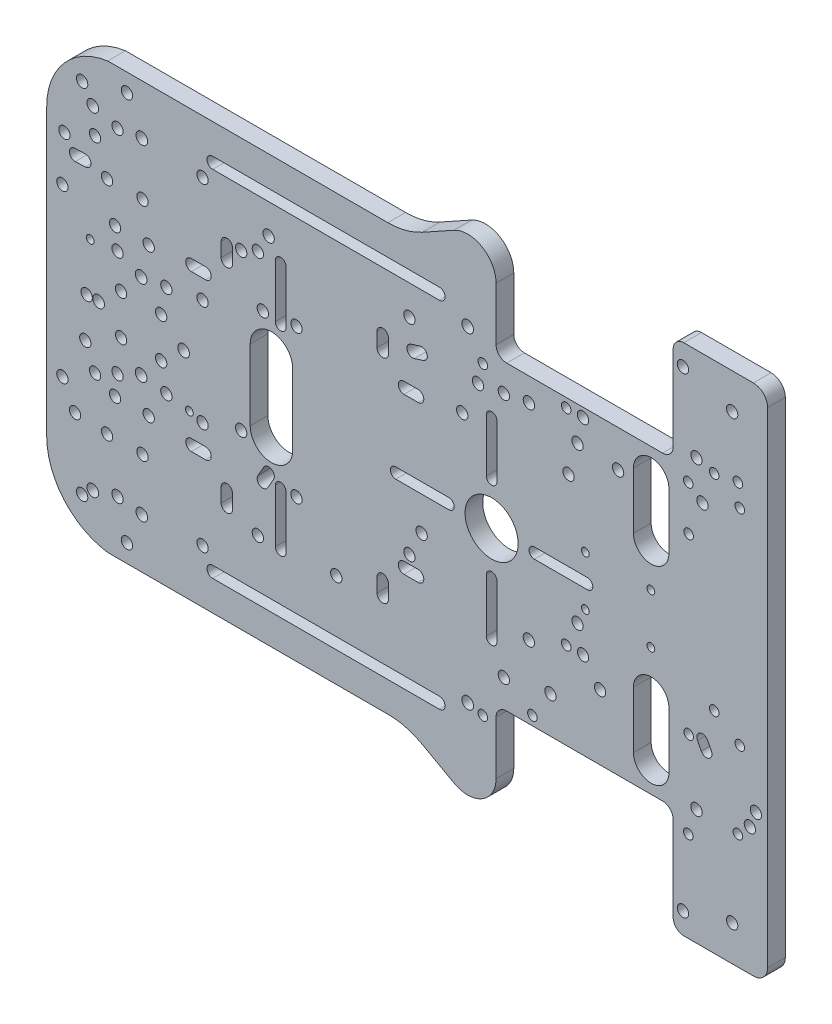
SolidWorks part; units mm, degrees
ref_plane "前视基准面" through (0, 0, 0) normal (0, 0, 1) x (1, 0, 0)
ref_plane "上视基准面" through (0, 0, 0) normal (0, 1, 0) x (1, 0, 0)
ref_plane "右视基准面" through (0, 0, 0) normal (1, 0, 0) x (0, 0, -1)
other "Configuration Table"
ref_plane "基准面1" through (0, 0, -5) normal (0, 0, -1) x (-1, 0, 0)
sketch "草图1" plane through (0, 0, -5) normal (0, 0, -1) x (-1, 0, 0)
  line L0 (-2.0302, 30.5969) -> (-4.5755, 31.4031)
  line L1 (-3.6092, 34.4537) -> (-1.064, 33.6476)
  line L2 (93.6948, 30.901) -> (90.7957, 31.001)
  line L3 (90.906, 34.199) -> (93.8052, 34.099)
  line L4 (-85.8731, -23.3852) -> (-84.789, -21.2965)
  line L5 (-81.9488, -22.7705) -> (-83.0328, -24.8593)
  line L6 (40.4887, -17.2053) -> (42.1253, -20.0649)
  line L7 (39.3479, -21.6544) -> (37.7113, -18.7947)
  line L8 (-63.8826, 34.7969) -> (-63.8826, 18.7969)
  line L9 (-73.8826, 18.7969) -> (-73.8826, 34.7969)
  line L10 (-73.8826, -34.7969) -> (-73.8826, -18.7969)
  line L11 (-63.8826, -18.7969) -> (-63.8826, -34.7969)
  line L12 (-35.9068, -1.5) -> (-50.9068, -1.5)
  line L13 (-50.9068, 1.5) -> (-35.9068, 1.5)
  line L14 (-11.7709, 1.5) -> (3.2291, 1.5)
  line L15 (3.2291, -1.5) -> (-11.7709, -1.5)
  line L16 (-25.3389, 12.0679) -> (-25.3389, 27.0679)
  line L17 (-22.3389, 27.0679) -> (-22.3389, 12.0679)
  line L18 (-25.3389, -27.0679) -> (-25.3389, -12.0679)
  line L19 (-22.3389, -12.0679) -> (-22.3389, -27.0679)
  line L20 (37.2135, -20) -> (37.2135, -35)
  line L21 (34.2135, -35) -> (34.2135, -20)
  line L22 (44.3046, 11) -> (44.3046, -9)
  line L23 (32.3046, -9) -> (32.3046, 11)
  line L24 (34.2135, 20) -> (34.2135, 35)
  line L25 (37.2135, 35) -> (37.2135, 20)
  line L27 (-25.0983, 69.5) -> (-25.0983, 45.53)
  line L28 (-28.0983, 42.53) -> (-72.0983, 42.53)
  line L29 (-75.0983, 45.53) -> (-75.0983, 69.5)
  line L30 (-78.0983, 72.5) -> (-81.75, 72.5)
  line L31 (-101.75, 52.5) -> (-101.75, -52.5)
  line L32 (-81.75, -72.5) -> (-78.0983, -72.5)
  line L33 (-75.0983, -69.5) -> (-75.0983, -45.53)
  line L34 (-72.0983, -42.53) -> (-28.0983, -42.53)
  line L35 (-25.0983, -45.53) -> (-25.0983, -69.5)
  line L38 (101.75, -40.2763) -> (101.75, 40.2763)
  line L40 (-81.75, 72.5) -> (-101.75, 72.5)
  line L41 (-101.75, 72.5) -> (-101.75, 52.5)
  line L42 (-101.75, -52.5) -> (-101.75, -72.5)
  line L43 (-101.75, -72.5) -> (-81.75, -72.5)
  line L44 (84.5216, 60.0833) -> (0.2583, 60.0833)
  line L46 (-22.0983, 72.5) -> (0.2583, 60.0833)
  line L47 (55, 0) -> (-55, 0) construction
  line L48 (-22.0983, -72.5) -> (0.2583, -60.0833)
  line L49 (-25.0983, -69.5) -> (-25.0983, -74.1662)
  line L50 (-22.0983, -72.5) -> (-25.0983, -74.1662)
  line L51 (84.5216, -60.0833) -> (0.2583, -60.0833)
  line L52 (-25.0983, 69.5) -> (-25.0983, 74.1662)
  line L53 (-22.0983, 72.5) -> (-25.0983, 74.1662)
  circle A0 centre (-27.2987, -34.7189) radius 1.6
  circle A1 centre (42.1392, -34.7189) radius 1.6
  circle A2 centre (42.1392, 34.7189) radius 1.6
  circle A3 centre (-27.2987, 34.7189) radius 1.6
  circle A4 centre (81.75, -45) radius 1.6
  circle A5 centre (88.1, -18) radius 1.6
  circle A6 centre (79.101, -55) radius 1.6
  circle A7 centre (93.75, -30.5) radius 1.6
  circle A8 centre (91.75, -49.5) radius 1.6
  circle A9 centre (-4.0924, -11.0716) radius 1.6
  circle A10 centre (-0.65, -18) radius 1.6
  circle A11 centre (31.2366, -19.8597) radius 1.6
  circle A12 centre (20, -33.5) radius 1.6
  circle A13 centre (-21.3568, -46.958) radius 1.35
  circle A14 centre (57.75, -45) radius 1.6
  circle A15 centre (31.2366, 21.8597) radius 1.6
  circle A16 centre (46.8508, 32.6) radius 1.6
  circle A17 centre (39.1, 40) radius 1.6
  circle A18 centre (-15.5471, 24.1222) radius 1.6
  circle A19 centre (-21.3568, 39.042) radius 1.35
  circle A20 centre (-20, 33.5) radius 1.6
  circle A21 centre (-0.65, 40) radius 1.6
  arc A22 (-4.5755, 31.4031) -> (-3.6092, 34.4537) centre (-4.0924, 32.9284) cw
  arc A23 (-1.064, 33.6476) -> (-2.0302, 30.5969) centre (-1.5471, 32.1222) cw
  circle A24 centre (57.75, -15) radius 1.6
  circle A25 centre (81.75, -15) radius 1.6
  circle A26 centre (90.8508, -11.4) radius 1.6
  circle A27 centre (57.75, 45) radius 1.6
  circle A28 centre (81.75, 45) radius 1.6
  circle A29 centre (88.1, 40) radius 1.6
  circle A30 centre (81.75, 15) radius 1.6
  circle A31 centre (57.75, 15) radius 1.6
  circle A32 centre (46.8508, -11.4) radius 1.6
  circle A33 centre (96.75, 36.5) radius 1.6
  circle A34 centre (79.101, 55) radius 1.6
  circle A35 centre (91.75, 51.5) radius 1.6
  arc A36 (93.8052, 34.099) -> (93.6948, 30.901) centre (93.75, 32.5) cw
  arc A37 (90.7957, 31.001) -> (90.906, 34.199) centre (90.8508, 32.6) cw
  circle A38 centre (-68.8, -6.5997) radius 1.1
  circle A39 centre (-68.8, 7.4003) radius 1.1
  circle A40 centre (-79.4702, 26.4708) radius 1.35
  circle A41 centre (-48.0924, 32.9284) radius 1.6
  circle A42 centre (-59.5471, 32.1222) radius 1.6
  circle A43 centre (-93.9, 40) radius 1.35
  circle A44 centre (-79.3568, 39.042) radius 1.35
  circle A45 centre (-44.9, 40) radius 1.35
  circle A46 centre (-49.65, 40) radius 1.6
  circle A47 centre (-91.75, 62.5) radius 1.6
  circle A48 centre (-83.3689, 35.9664) radius 1.6
  circle A49 centre (-77.8574, 66.5) radius 1.6
  circle A50 centre (-86.675, 44.8459) radius 1.35
  circle A51 centre (-79.3568, -46.958) radius 1.35
  circle A52 centre (-81.6777, -39.8031) radius 1.6
  circle A53 centre (-35.3568, -39.958) radius 1.35
  circle A54 centre (-34.369, -22.0335) radius 1.6
  circle A55 centre (-93.3568, -39.958) radius 1.35
  circle A56 centre (-91.75, -62.5) radius 1.6
  circle A57 centre (-77.8574, -66.5) radius 1.6
  circle A58 centre (-40.4529, -32.1222) radius 1.6
  circle A59 centre (-98.4529, -32.1222) radius 1.6
  arc A60 (-84.789, -21.2965) -> (-81.9488, -22.7705) centre (-83.3689, -22.0335) cw
  arc A61 (-83.0328, -24.8593) -> (-85.8731, -23.3852) centre (-84.4529, -24.1222) cw
  circle A62 centre (-79.4702, -22.5291) radius 1.35
  circle A63 centre (-96.75, -36.5) radius 1.6
  circle A64 centre (-93.3568, 46.042) radius 1.35
  circle A65 centre (-81.6777, 46.1969) radius 1.6
  circle A66 centre (-86.675, -13.154) radius 1.35
  circle A67 centre (-93.9, -18) radius 1.35
  circle A68 centre (-48.0924, -11.0716) radius 1.6
  circle A69 centre (-50.3001, -6.5997) radius 1.1
  circle A70 centre (-50.3001, 7.4003) radius 1.1
  circle A71 centre (-49.65, -18) radius 1.6
  circle A72 centre (-45.5471, 24.1222) radius 1.6
  circle A73 centre (-44.9, -18) radius 1.35
  circle A74 centre (-54.4529, -24.1222) radius 1.6
  circle A75 centre (-34.369, 35.9664) radius 1.6
  arc A76 (42.1253, -20.0649) -> (39.3479, -21.6544) centre (40.7366, -20.8597) cw
  arc A77 (37.7113, -18.7947) -> (40.4887, -17.2053) centre (39.1, -18) cw
  circle A78 centre (80.7531, 5.6569) radius 1.6
  circle A79 centre (82.4559, 20.8597) radius 1.6
  circle A80 centre (89.4709, 14.0014) radius 1.1
  circle A81 centre (67.9702, 12.9897) radius 1.6
  circle A82 centre (97.3184, 23.5) radius 1.6
  circle A83 centre (40.7366, 20.8597) radius 1.6
  circle A84 centre (72.9559, 20.8597) radius 1.6
  circle A85 centre (74.7057, -31.2) radius 1.6
  circle A86 centre (72.9559, -20.8597) radius 1.6
  circle A87 centre (74.7057, 31.2) radius 1.6
  circle A88 centre (67.9702, -12.9897) radius 1.6
  circle A89 centre (69.4394, 5.6569) radius 1.6
  circle A90 centre (80.7531, -5.6569) radius 1.6
  circle A91 centre (84.7052, -31.2) radius 1.6
  circle A92 centre (90.4702, 0.0007) radius 1.6
  circle A93 centre (69.4394, -5.6569) radius 1.6
  circle A94 centre (84.7052, 31.2) radius 1.6
  circle A95 centre (82.4559, -20.8597) radius 1.6
  circle A96 centre (61.4695, -14) radius 1.1
  circle A97 centre (97.3184, -23.5) radius 1.6
  arc A98 (-73.8826, 34.7969) -> (-63.8826, 34.7969) centre (-68.8826, 34.7969) cw
  arc A99 (-63.8826, 18.7969) -> (-73.8826, 18.7969) centre (-68.8826, 18.7969) cw
  arc A100 (-63.8826, -34.7969) -> (-73.8826, -34.7969) centre (-68.8826, -34.7969) cw
  arc A101 (-73.8826, -18.7969) -> (-63.8826, -18.7969) centre (-68.8826, -18.7969) cw
  arc A102 (-50.9068, -1.5) -> (-50.9068, 1.5) centre (-50.9068, 0) cw
  arc A103 (-35.9068, 1.5) -> (-35.9068, -1.5) centre (-35.9068, 0) cw
  arc A104 (3.2291, 1.5) -> (3.2291, -1.5) centre (3.2291, 0) cw
  arc A105 (-11.7709, -1.5) -> (-11.7709, 1.5) centre (-11.7709, 0) cw
  circle A106 centre (-23.8389, 0) radius 7.5
  arc A107 (-25.3389, 27.0679) -> (-22.3389, 27.0679) centre (-23.8389, 27.0679) cw
  arc A108 (-22.3389, 12.0679) -> (-25.3389, 12.0679) centre (-23.8389, 12.0679) cw
  arc A109 (-25.3389, -12.0679) -> (-22.3389, -12.0679) centre (-23.8389, -12.0679) cw
  arc A110 (-22.3389, -27.0679) -> (-25.3389, -27.0679) centre (-23.8389, -27.0679) cw
  arc A111 (37.2135, -35) -> (34.2135, -35) centre (35.7135, -35) cw
  arc A112 (34.2135, -20) -> (37.2135, -20) centre (35.7135, -20) cw
  arc A113 (32.3046, 11) -> (44.3046, 11) centre (38.3046, 11) cw
  arc A114 (44.3046, -9) -> (32.3046, -9) centre (38.3046, -9) cw
  arc A115 (34.2135, 35) -> (37.2135, 35) centre (35.7135, 35) cw
  arc A116 (37.2135, 20) -> (34.2135, 20) centre (35.7135, 20) cw
  arc A118 (-25.0983, 45.53) -> (-28.0983, 42.53) centre (-28.0983, 45.53) cw
  arc A119 (-72.0983, 42.53) -> (-75.0983, 45.53) centre (-72.0983, 45.53) cw
  arc A120 (-75.0983, 69.5) -> (-78.0983, 72.5) centre (-78.0983, 69.5) ccw
  arc A123 (-78.0983, -72.5) -> (-75.0983, -69.5) centre (-78.0983, -69.5) ccw
  arc A124 (-75.0983, -45.53) -> (-72.0983, -42.53) centre (-72.0983, -45.53) cw
  arc A125 (-28.0983, -42.53) -> (-25.0983, -45.53) centre (-28.0983, -45.53) cw
  arc A128 (84.5216, -60.0833) -> (101.75, -40.2763) centre (81.75, -40.2763) ccw
  arc A129 (101.75, 40.2763) -> (84.5216, 60.0833) centre (81.75, 40.2763) ccw
  dimension "D1" = 180
extrude "凸台-拉伸1" add sketch "草图1" against normal blind 5
sketch "草图2" plane through (0, 0, -5) normal (0, 0, -1) x (-1, 0, 0)
  circle A0 centre (75.0963, 12) radius 1.65
  circle A1 centre (87.0963, 0) radius 1.65
  circle A2 centre (75.0963, -12) radius 1.65
  circle A3 centre (63.0963, 0) radius 1.65
extrude "切除-拉伸1" cut sketch "草图2" against normal blind 10
sketch "草图3" plane through (0, 0, -5) normal (0, 0, -1) x (-1, 0, 0)
  circle A0 centre (88.75, 47) radius 1.65
  circle A1 centre (88.75, -47) radius 1.65
extrude "切除-拉伸2" cut sketch "草图3" against normal blind 10
fillet "圆角1" radius 4 2 edges at (101.75, -72.5, -2.5) (101.75, 72.5, -2.5)
fillet "圆角2" radius 8 2 edges at (25.0983, 74.1662, -2.5) (25.0983, -74.1662, -2.5)
fillet "圆角3" radius 20 2 edges at (-0.2583, -60.0833, -2.5) (-0.2583, 60.0833, -2.5)
sketch "草图4" plane through (0, 0, -5) normal (0, 0, -1) x (-1, 0, 0)
  line L0 (101.75, 0) -> (-23.8389, 0) construction
  line L1 (6.9017, 32) -> (6.9017, 28) construction
  line L2 (-25.0983, 60.572) -> (-25.0983, 45.53) construction
  line L3 (74.9017, -46) -> (-17.0983, -46) construction
  line L4 (74.9017, -46) -> (74.9017, 46) construction
  line L5 (74.9017, 46) -> (-17.0983, 46) construction
  line L6 (-17.0983, -46) -> (-17.0983, 46) construction
  line L7 (28.9017, 46) -> (28.9017, -46) construction
  line L8 (101.75, -40.2763) -> (101.75, 40.2763) construction
  line L9 (8.5017, 32) -> (8.5017, 28)
  line L10 (6.9017, 32) -> (50.9017, 32) construction
  line L11 (6.9017, 32) -> (6.9017, -32) construction
  line L12 (6.9017, -32) -> (50.9017, -32) construction
  line L13 (50.9017, 32) -> (50.9017, -32) construction
  line L14 (28.9017, -32) -> (28.9017, 32) construction
  line L16 (-3.0983, 22) -> (60.9017, 22) construction
  line L17 (-3.0983, 22) -> (-3.0983, -22) construction
  line L18 (-3.0983, -22) -> (60.9017, -22) construction
  line L19 (60.9017, 22) -> (60.9017, -22) construction
  line L20 (28.9017, -22) -> (28.9017, 22) construction
  line L21 (-3.0983, 0) -> (60.9017, 0) construction
  line L22 (6.9017, 16.0659) -> (6.9017, -16.0659) construction
  line L24 (50.9017, 16.0659) -> (50.9017, -16.0659) construction
  line L25 (28.9017, -16.0659) -> (28.9017, 16.0659) construction
  line L26 (6.9017, 0) -> (50.9017, 0) construction
  line L27 (5.3017, 32) -> (5.3017, 28)
  line L28 (-3.0983, 22) -> (0.9017, 22) construction
  line L29 (-3.0983, 23.6) -> (0.9017, 23.6)
  line L30 (-3.0983, 20.4) -> (0.9017, 20.4)
  line L31 (60.9017, 22) -> (56.9017, 22) construction
  line L32 (60.9017, 23.6) -> (56.9017, 23.6)
  line L33 (60.9017, 20.4) -> (56.9017, 20.4)
  line L34 (50.9017, 32) -> (50.9017, 28) construction
  line L35 (49.3017, 32) -> (49.3017, 28)
  line L36 (52.5017, 32) -> (52.5017, 28)
  line L37 (60.9017, -22) -> (56.9017, -22) construction
  line L38 (60.9017, -23.6) -> (56.9017, -23.6)
  line L39 (60.9017, -20.4) -> (56.9017, -20.4)
  line L40 (50.9017, -32) -> (50.9017, -28) construction
  line L41 (49.3017, -32) -> (49.3017, -28)
  line L42 (52.5017, -32) -> (52.5017, -28)
  line L43 (-3.0983, -22) -> (0.9017, -22) construction
  line L44 (-3.0983, -23.6) -> (0.9017, -23.6)
  line L45 (-3.0983, -20.4) -> (0.9017, -20.4)
  line L46 (6.9017, -32) -> (6.9017, -28) construction
  line L47 (8.5017, -32) -> (8.5017, -28)
  line L48 (5.3017, -32) -> (5.3017, -28)
  circle A0 centre (-17.0983, 46) radius 1.65
  arc A2 (8.5017, 32) -> (5.3017, 32) centre (6.9017, 32) ccw
  circle A6 centre (74.9017, 46) radius 1.65
  circle A7 centre (74.9017, -46) radius 1.65
  circle A12 centre (-17.0983, -46) radius 1.65
  arc A13 (5.3017, 28) -> (8.5017, 28) centre (6.9017, 28) ccw
  arc A14 (-3.0983, 23.6) -> (-3.0983, 20.4) centre (-3.0983, 22) ccw
  arc A15 (0.9017, 20.4) -> (0.9017, 23.6) centre (0.9017, 22) ccw
  arc A16 (60.9017, 23.6) -> (60.9017, 20.4) centre (60.9017, 22) cw
  arc A17 (56.9017, 20.4) -> (56.9017, 23.6) centre (56.9017, 22) cw
  arc A18 (49.3017, 32) -> (52.5017, 32) centre (50.9017, 32) cw
  arc A19 (52.5017, 28) -> (49.3017, 28) centre (50.9017, 28) cw
  arc A20 (60.9017, -23.6) -> (60.9017, -20.4) centre (60.9017, -22) ccw
  arc A21 (56.9017, -20.4) -> (56.9017, -23.6) centre (56.9017, -22) ccw
  arc A22 (49.3017, -32) -> (52.5017, -32) centre (50.9017, -32) ccw
  arc A23 (52.5017, -28) -> (49.3017, -28) centre (50.9017, -28) ccw
  arc A24 (-3.0983, -23.6) -> (-3.0983, -20.4) centre (-3.0983, -22) cw
  arc A25 (0.9017, -20.4) -> (0.9017, -23.6) centre (0.9017, -22) cw
  arc A26 (8.5017, -32) -> (5.3017, -32) centre (6.9017, -32) cw
  arc A27 (5.3017, -28) -> (8.5017, -28) centre (6.9017, -28) cw
  point P2 (6.9017, 30)
  point P5 (28.9017, 0)
  point P11 (28.9017, 0)
  point P15 (28.9017, 0)
  point P27 (-1.0983, 22)
  point P31 (28.9017, 0)
  point P39 (58.9017, 22)
  point P45 (50.9017, 30)
  point P51 (58.9017, -22)
  point P57 (50.9017, -30)
  point P63 (-1.0983, -22)
  point P69 (6.9017, -30)
  dimension "D8" = 3.3
  dimension "D9" = 1.6
  dimension "D10" = 4
  dimension "D12" = 1.6
  dimension "D1" = 92
  dimension "D2" = 92
  dimension "D3" = 8
  dimension "D4" = 64
  dimension "D5" = 44
  dimension "D6" = 64
  dimension "D7" = 44
  dimension "D11" = 4
extrude "切除-拉伸3" cut sketch "草图4" against normal blind 10
sketch "草图5" plane through (0, 0, -5) normal (0, 0, -1) x (-1, 0, 0)
  line L0 (-23.8389, 0) -> (101.75, 0) construction
  line L1 (101.75, -40.2763) -> (101.75, 40.2763) construction
  line L2 (-25.0983, 50) -> (99.2271, 50) construction
  line L3 (-25.0983, 60.572) -> (-25.0983, 45.53) construction
  line L4 (-9.0983, 50) -> (54.9017, 50) construction
  line L5 (-9.0983, 51.6) -> (54.9017, 51.6)
  line L6 (-9.0983, 48.4) -> (54.9017, 48.4)
  line L7 (-9.0983, -50) -> (54.9017, -50) construction
  line L8 (-9.0983, -51.6) -> (54.9017, -51.6)
  line L9 (-9.0983, -48.4) -> (54.9017, -48.4)
  arc A0 (101.75, 40.2763) -> (84.5216, 60.0833) centre (81.75, 40.2763) ccw construction
  arc A1 (-9.0983, 51.6) -> (-9.0983, 48.4) centre (-9.0983, 50) ccw
  arc A2 (54.9017, 48.4) -> (54.9017, 51.6) centre (54.9017, 50) ccw
  arc A3 (-9.0983, -51.6) -> (-9.0983, -48.4) centre (-9.0983, -50) cw
  arc A4 (54.9017, -48.4) -> (54.9017, -51.6) centre (54.9017, -50) cw
  point P14 (22.9017, 50)
  point P21 (22.9017, -50)
  dimension "D2" = 1.6
  dimension "D3" = 16
  dimension "D1" = 64
  dimension "D4" = 100
extrude "切除-拉伸4" cut sketch "草图5" against normal blind 10
